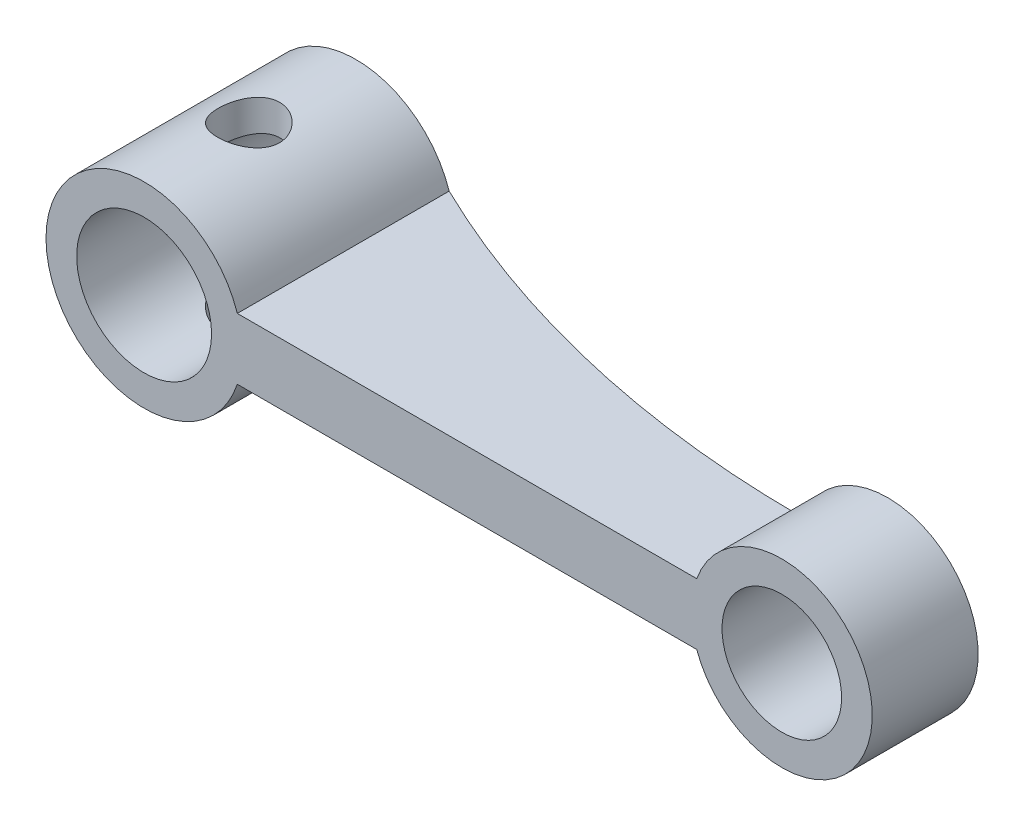
SolidWorks part; units mm, degrees
material "ABS"
ref_plane "Front Plane" through (0, 0, 0) normal (0, 0, 1) x (1, 0, 0)
ref_plane "Top Plane" through (0, 0, 0) normal (0, 1, 0) x (1, 0, 0)
ref_plane "Right Plane" through (0, 0, 0) normal (1, 0, 0) x (0, 0, -1)
sketch "Sketch1" plane through (0, 0, 0) normal (0, 0, 1) x (1, 0, 0)
  line L0 (0, 0) -> (-20.8, 0) construction
  line L3 (-17.7603, -1) -> (-2.7753, -1)
  line L5 (-17.7603, 1) -> (-2.7753, 1)
  line L13 (0, -2.95) -> (0, 2.95) construction
  circle A0 centre (0, 0) radius 1.95
  arc A1 (-2.7753, -1) -> (-2.7753, 1) centre (0, 0) ccw
  circle A3 centre (-20.8, 0) radius 2.2
  arc A6 (-17.7603, 1) -> (-17.7603, -1) centre (-20.8, 0) ccw
  dimension "D1" = 20.8
  dimension "D2" = 2.95
  dimension "D3" = 1
  dimension "D4" = 3.9
  dimension "D7" = 4.4
  dimension "D8" = 1
  dimension "D5" = 2
  dimension "D6" = 1
extrude "main body" add sketch "Sketch1" along normal blind 6.91
sketch "Sketch2" plane through (0, -1, 0) normal (0, -1, 0) x (1, 0, 0)
  line L6 (-20.8, 6.91) -> (-20.8801, 0) construction
  line L7 (-18.6, 6.91) -> (-23, 6.91) construction
  line L8 (-24, 0) -> (-17.7603, 0) construction
  circle A0 centre (-20.8401, 3.455) radius 1
  dimension "D1" = 2
extrude "tendon hole" cut sketch "Sketch2" against normal mid plane 20
sketch "Sketch3" plane through (0, -1, 0) normal (0, -1, 0) x (1, 0, 0)
  line L0 (-17.7603, 3.455) -> (-2.7753, 3.455) construction
  line L1 (-17.7603, 6.91) -> (-17.7603, 0) construction
  line L2 (-2.7753, 6.91) -> (-2.7753, 0) construction
  line L3 (-2.7753, 3.455) -> (2.95, 3.455)
  line L4 (2.95, 0) -> (2.95, 6.91) construction
  line L5 (2.95, 3.455) -> (2.95, 0)
  line L6 (2.95, 0) -> (-2.7753, 0)
  line L7 (-2.7753, 0) -> (-2.7753, 3.455) construction
  line L8 (-17.7603, 0) -> (-2.7753, 0)
  line L9 (-17.7603, 0) -> (-2.7753, 3.455) construction
  arc A0 (-17.7603, 0) -> (-2.7753, 3.455) centre (-17.7603, 34.2236) ccw construction
  arc A1 (-17.7603, 0) -> (-2.7753, 3.455) centre (-2.7753, -30.7686) cw
extrude "material removal" cut sketch "Sketch3" against normal mid plane 10
